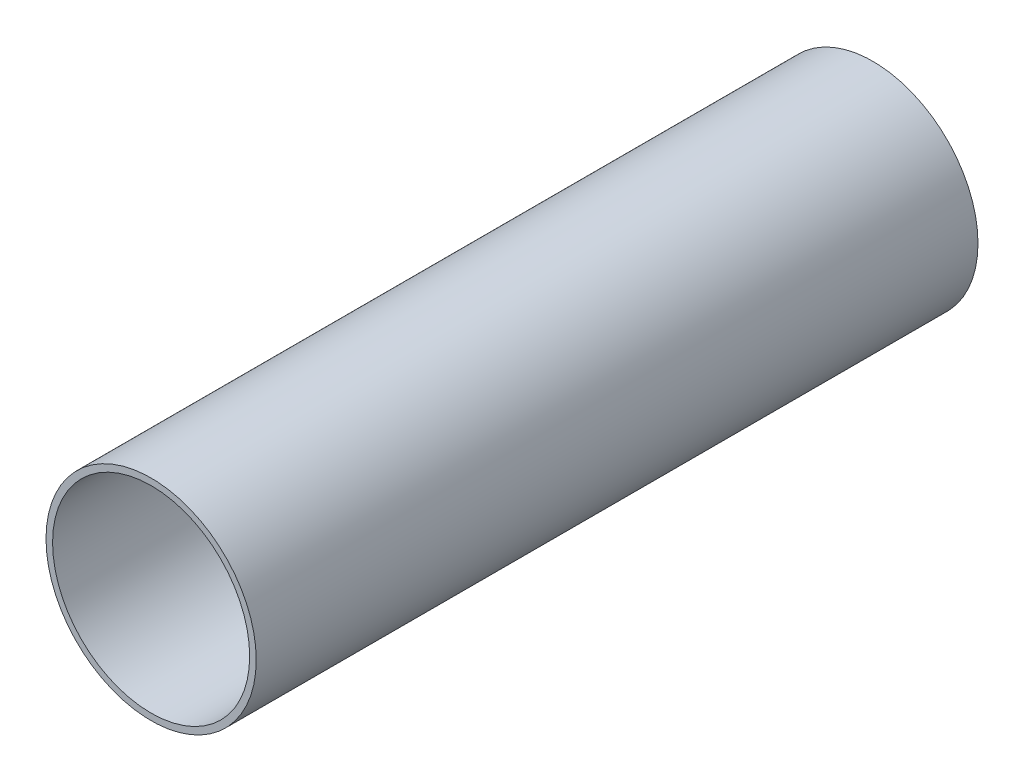
SolidWorks part; units mm, degrees
ref_plane "Front" through (0, 0, 0) normal (0, 0, 1) x (1, 0, 0)
ref_plane "Top" through (0, 0, 0) normal (0, 1, 0) x (1, 0, 0)
ref_plane "Side" through (0, 0, 0) normal (1, 0, 0) x (0, 0, -1)
sketch "PipeSketch" plane through (0, 0, 0) normal (0, 0, 1) x (1, 0, 0)
  circle A0 centre (0, 0) radius 304.8
  circle A1 centre (0, 0) radius 285.75
  dimension "OuterDiameter" = 609.6
  dimension "InnerDiameter" = 571.5
extrude "Extrusion" add sketch "PipeSketch" along normal blind 2092.8
sketch "FilterSketch" plane through (0, 0, 0) normal (0, 0, 1) x (1, 0, 0)
  circle A0 centre (0, 0) radius 304.8 construction
  dimension "NominalDiameter" = 609.6
